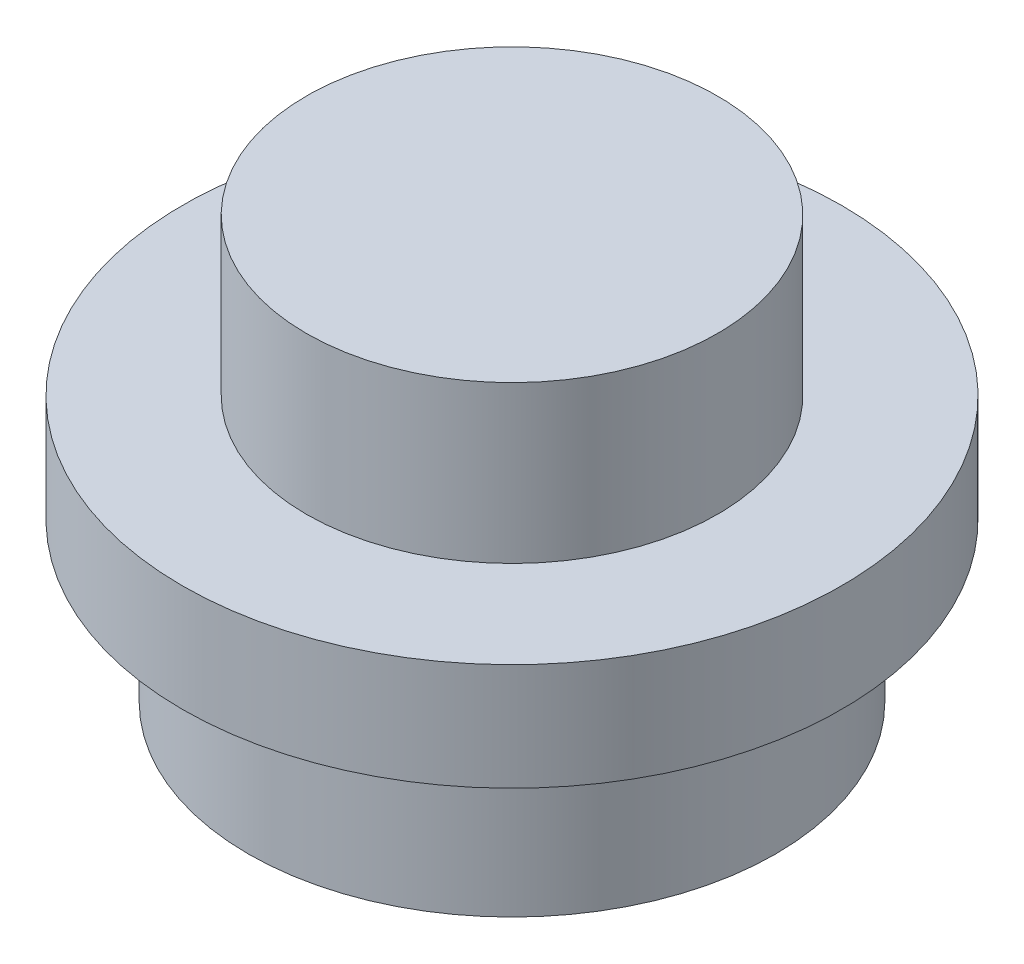
SolidWorks part; units mm, degrees
ref_plane "Front Plane" through (0, 0, 0) normal (0, 0, 1) x (1, 0, 0)
ref_plane "Top Plane" through (0, 0, 0) normal (0, 1, 0) x (1, 0, 0)
ref_plane "Right Plane" through (0, 0, 0) normal (1, 0, 0) x (0, 0, -1)
sketch "Sketch1" plane through (0, 0, 0) normal (0, 0, 1) x (1, 0, 0)
  line L0 (-0.4559, 2.159) -> (-2.8371, 2.159)
  line L1 (-2.8371, 2.159) -> (-2.8371, 0)
  line L2 (-2.8371, 0) -> (-3.6309, 0)
  line L3 (-3.6309, 0) -> (-3.6309, 1.905)
  line L4 (-3.6309, 1.905) -> (-4.4246, 1.905)
  line L5 (-4.4246, 1.905) -> (-4.4246, 3.1937)
  line L6 (-4.4246, 3.1937) -> (-2.9324, 3.1937)
  line L7 (-2.9324, 3.1937) -> (-2.9324, 5.08)
  line L8 (-2.9324, 5.08) -> (-0.4559, 5.08)
  line L9 (-0.4559, 5.08) -> (-0.4559, 2.159) construction
  line L10 (-0.4559, 2.159) -> (-0.4559, 5.08)
  point P8 (-4.0278, 1.905)
  dimension "D1" = 4.7625
  dimension "D2" = 6.35
  dimension "D3" = 5.08
  dimension "D4" = 2.159
  dimension "D5" = 1.905
  dimension "D6" = 7.9375
  dimension "D7" = 4.953
revolve "Revolve1" add sketch "Sketch1" angle 360 about L9
